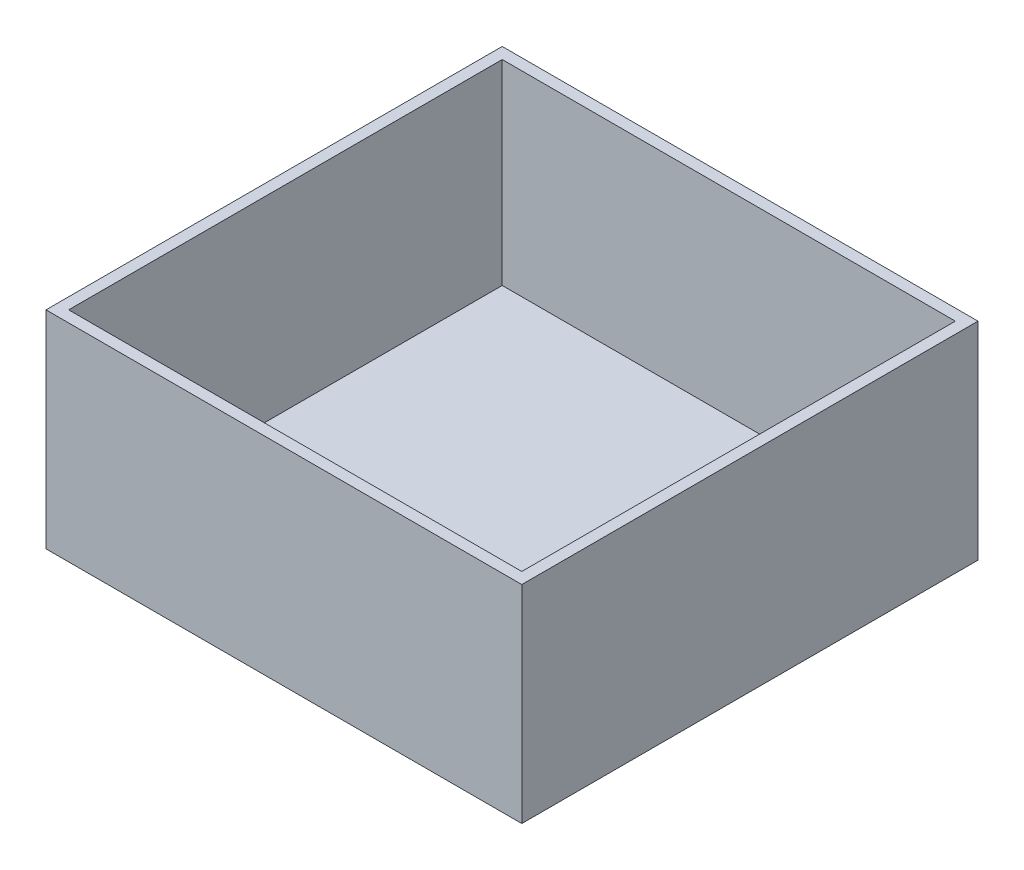
SolidWorks part; units mm, degrees
ref_plane "Front Plane" through (0, 0, 0) normal (0, 0, 1) x (1, 0, 0)
ref_plane "Top Plane" through (0, 0, 0) normal (0, 1, 0) x (1, 0, 0)
ref_plane "Right Plane" through (0, 0, 0) normal (1, 0, 0) x (0, 0, -1)
sketch "Sketch1" plane through (0, 0, 0) normal (0, 1, 0) x (1, 0, 0)
  line L1 (0, 0) -> (117.348, 0)
  line L2 (0, 0) -> (0, 112.522)
  line L3 (0, 112.522) -> (117.348, 112.522)
  line L4 (117.348, 0) -> (117.348, 112.522)
  dimension "D1" = 117.348
  dimension "D2" = 112.522
extrude "Boss-Extrude1" add sketch "Sketch1" along normal blind 2.794
sketch "Sketch3" plane through (0, 2.794, 0) normal (0, 1, 0) x (1, 0, 0)
  line L1 (0, 0) -> (114.554, 0)
  line L2 (0, 0) -> (0, 2.794)
  line L3 (0, 2.794) -> (114.554, 2.794)
  line L4 (114.554, 0) -> (114.554, 2.794)
  dimension "D1" = 2.794
  dimension "D2" = 114.554
extrude "Boss-Extrude2" add sketch "Sketch3" along normal blind 48.26
pattern_linear "LPattern1" count 2 spacing 109.728 along (0, 0, -1) of "Boss-Extrude2"
sketch "Sketch4" plane through (0, 2.794, 0) normal (0, 1, 0) x (1, 0, 0)
  line L0 (114.554, 2.794) -> (0, 2.794) construction
  line L1 (0, 109.728) -> (2.794, 109.728)
  line L2 (0, 109.728) -> (0, 2.794)
  line L3 (0, 2.794) -> (2.794, 2.794)
  line L4 (2.794, 109.728) -> (2.794, 2.794)
  dimension "D1" = 2.794
extrude "Boss-Extrude3" add sketch "Sketch4" along normal blind 48.26
sketch "Sketch6" plane through (0, 2.794, 0) normal (0, 1, 0) x (1, 0, 0)
  line L0 (-28.0797, 0) -> (28.0797, 0) construction
  line L1 (117.348, 112.522) -> (114.554, 112.522)
  line L2 (117.348, 112.522) -> (117.348, 0)
  line L3 (117.348, 0) -> (114.554, 0)
  line L4 (114.554, 112.522) -> (114.554, 0)
extrude "Boss-Extrude4" add sketch "Sketch6" along normal blind 48.26
sketch "Sketch9" plane through (117.348, 0, 0) normal (1, 0, 0) x (0, 0, -1)
  line L0 (0, 28.0797) -> (0, -28.0797) construction
  line L1 (0, 36.0675) -> (112.522, 36.0675)
  line L2 (0, 36.0675) -> (0, 23.1135)
  line L3 (0, 23.1135) -> (112.522, 23.1135)
  line L4 (112.522, 36.0675) -> (112.522, 23.1135)
  line L5 (112.522, 51.054) -> (112.522, 0) construction
  dimension "D1" = 12.954
equation "\"4.1.5in\"=4.37"
